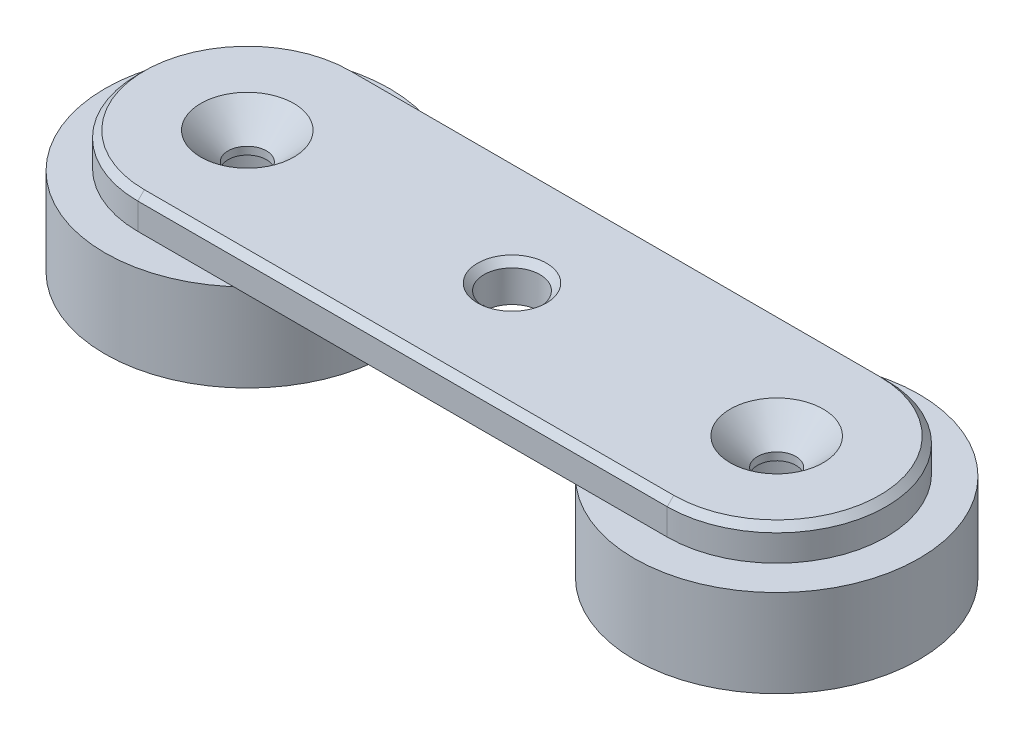
SolidWorks part; units mm, degrees
other "Rotor_1"
other "Rotor_2" parameters "D1"=10.994, "D3"=11.0231, "D4"=5, "D2"=144
ref_plane "Front Plane" through (0, 0, 0) normal (0, 0, 1) x (1, 0, 0)
ref_plane "Top Plane" through (0, 0, 0) normal (0, 1, 0) x (1, 0, 0)
ref_plane "Right Plane" through (0, 0, 0) normal (1, 0, 0) x (0, 0, -1)
sketch "Sketch1" plane through (0, 0, 0) normal (0, 1, 0) x (1, 0, 0)
  line L0 (24.175, 0) -> (-24.175, 0) construction
  line L1 (24.175, -10) -> (-24.175, -10)
  line L2 (24.175, 10) -> (-24.175, 10)
  arc A0 (24.175, -10) -> (24.175, 10) centre (24.175, 0) ccw
  arc A1 (-24.175, 10) -> (-24.175, -10) centre (-24.175, 0) ccw
  circle A2 centre (0, 0) radius 2.55
  circle A3 centre (-24.175, 0) radius 5 construction
  circle A4 centre (24.175, 0) radius 5 construction
  point P2 (0, 0)
  dimension "D1" = 10
  dimension "D3" = 5.1
  dimension "D4" = 10
  dimension "D2" = 48.35
extrude "Boss-Extrude1" add sketch "Sketch1" along normal blind 3
sketch "Sketch10" plane through (0, 3, 0) normal (0, 1, 0) x (1, 0, 0)
  circle A0 centre (-24.175, 0) radius 7.5
  circle A1 centre (24.175, 0) radius 7.5
  dimension "D1" = 15
extrude "Boss-Extrude6" add sketch "Sketch10" along normal blind 0.2
sketch "Sketch11" plane through (0, 3.2, 0) normal (0, 1, 0) x (1, 0, 0)
  circle A0 centre (-24.175, 0) radius 5.05
  circle A1 centre (24.175, 0) radius 5.05
  dimension "D1" = 10.1
extrude "Boss-Extrude8" add sketch "Sketch11" along normal blind 8
sketch "Sketch12" plane through (0, 3.2, 0) normal (0, 1, 0) x (1, 0, 0)
  circle A0 centre (-24.175, 0) radius 5
  circle A1 centre (-24.175, 0) radius 13
  dimension "D1" = 26
  dimension "D2" = 10
extrude "Boss-Extrude9" add sketch "Sketch12" along normal blind 8 separate body
mirror "Mirror3" about plane through (0, 0, 0) normal (1, 0, 0) of bodies 113
sketch "Sketch13" plane through (0, 11.2, 0) normal (0, 1, 0) x (1, 0, 0)
  circle A0 centre (-24.175, 0) radius 1.25
  circle A1 centre (24.175, 0) radius 1.25
  dimension "D1" = 2.5
extrude "Cut-Extrude6" cut sketch "Sketch13" against normal through all
ref_plane "Plane1" through (0, 11.4, 0) normal (0, 1, 0) x (1, 0, 0)
sketch "Sketch14" plane through (0, 11.4, 0) normal (0, 1, 0) x (1, 0, 0)
  line L2 (-24.175, -10) -> (24.175, -10)
  line L3 (24.175, 10) -> (-24.175, 10)
  line L4 (-24.175, -10) -> (24.175, -10)
  line L5 (24.175, 10) -> (-24.175, 10)
  circle A0 centre (0, 0) radius 2.55 construction
  circle A1 centre (0, 0) radius 2.55
  arc A2 (24.175, -10) -> (24.175, 10) centre (24.175, 0) ccw
  arc A3 (-24.175, 10) -> (-24.175, -10) centre (-24.175, 0) ccw
  arc A4 (24.175, -10) -> (24.175, 10) centre (24.175, 0) ccw
  arc A5 (-24.175, 10) -> (-24.175, -10) centre (-24.175, 0) ccw
  circle A8 centre (-24.175, 0) radius 1.75
  circle A9 centre (24.175, 0) radius 1.75
  dimension "D2" = 3.5
  dimension "D1" = 0
extrude "Boss-Extrude10" add sketch "Sketch14" along normal blind 3 separate body
sketch "Sketch15" plane through (0, 11.4, 0) normal (0, -1, 0) x (1, 0, 0)
  circle A2 centre (24.175, 0) radius 7.5 construction
  circle A3 centre (-24.175, 0) radius 7.5 construction
  circle A4 centre (-24.175, 0) radius 1.75 construction
  circle A5 centre (24.175, 0) radius 1.75 construction
  circle A6 centre (24.175, 0) radius 7.5
  circle A7 centre (-24.175, 0) radius 7.5
  circle A8 centre (-24.175, 0) radius 1.75
  circle A9 centre (24.175, 0) radius 1.75
extrude "Boss-Extrude11" add sketch "Sketch15" along normal blind 0.2
chamfer "Chamfer1" distance 2.5 angle 45 2 edges at (-24.175, 14.4, 1.75) (24.175, 14.4, 1.75)
chamfer "Chamfer2" distance 0.6 angle 45 5 edges at (0, 14.4, 10) (34.175, 14.4, 0) (-34.175, 14.4, 0) (0, 14.4, -10) (0, 14.4, 2.55)
sketch "Sketch16" plane through (0, 3, 0) normal (0, 1, 0) x (1, 0, 0)
  line L0 (-10, 0) -> (-2.55, 0)
  line L1 (2.55, 0) -> (10, 0)
  arc A0 (10, 0) -> (-10, 0) centre (0, 0) ccw
  circle A1 centre (0, 0) radius 2.55 construction
  arc A2 (2.55, 0) -> (-2.55, 0) centre (0, 0) ccw
  dimension "D1" = 20
extrude "Boss-Extrude12" add sketch "Sketch16" along normal blind 0.5
sketch "Sketch17" plane through (0, 11.4, 0) normal (0, -1, 0) x (1, 0, 0)
  line L4 (-2.55, 0) -> (-10, 0)
  line L5 (10, 0) -> (2.55, 0)
  line L6 (-2.55, 0) -> (-10, 0)
  line L7 (10, 0) -> (2.55, 0)
  arc A5 (-10, 0) -> (10, 0) centre (0, 0) ccw
  arc A6 (-2.55, 0) -> (2.55, 0) centre (0, 0) ccw
  arc A8 (-10, 0) -> (10, 0) centre (0, 0) ccw
  arc A9 (-2.55, 0) -> (2.55, 0) centre (0, 0) ccw
  dimension "D1" = 0
extrude "Boss-Extrude13" add sketch "Sketch17" along normal blind 0.5
chamfer "Chamfer3" distance 0.6 angle 45 7 edges at (24.175, 0, 1.25) (0, 0, 2.55) (-24.175, 0, 1.25) (34.175, 0, 0) (0, 0, -10) (0, 0, 10) (-34.175, 0, 0)
delete or keep bodies "Body-Delete/Keep 1" type delete bodies bodies 118
delete or keep bodies "Body-Delete/Keep 2" [suppressed] type delete bodies bodies 119
equation "\"D2@Sketch1\"=74.35-26"
